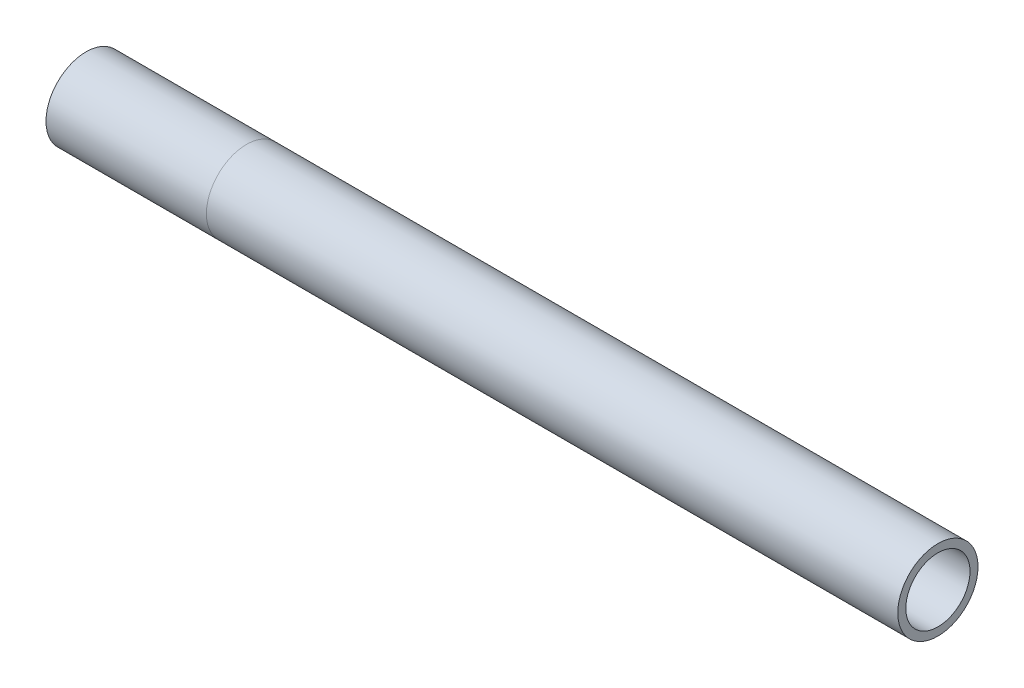
SolidWorks part; units mm, degrees
ref_plane "Front Plane" through (0, 0, 0) normal (0, 0, 1) x (1, 0, 0)
ref_plane "Top Plane" through (0, 0, 0) normal (0, 1, 0) x (1, 0, 0)
ref_plane "Right Plane" through (0, 0, 0) normal (1, 0, 0) x (0, 0, -1)
sketch "Sketch2" plane through (0, 0, 0) normal (0, 0, 1) x (1, 0, 0)
  line L0 (-77.8723, 14.641) -> (125.953, 14.641) construction
  line L1 (-107.3181, 25.8935) -> (-56.5181, 25.8935)
  line L2 (-56.5181, 25.8935) -> (162.4299, 25.8935)
  line L3 (162.4299, 25.8935) -> (162.4299, -141.1032) construction
  line L4 (-56.5181, 25.8935) -> (-56.5181, -136.7296) construction
  line L5 (189.8569, 74.1051) -> (189.8569, -336.1283) construction
  dimension "D1" = 180
  dimension "D2" = 50.8
  dimension "D3" = 218.948
ref_plane "Plane1" through (-107.3181, 25.8935, 0) normal (1, 0, 0) x (0, 1, 0)
ref_plane "Plane2" through (-56.5181, 25.8935, 0) normal (1, 0, 0) x (0, 1, 0)
other "Tubing TUBING(1)"
ref_plane "Plane3" through (-107.3181, 25.8935, 0) normal (1, 0, 0) x (0, 1, 0)
sketch "Sketch1" plane through (-107.3181, 25.8935, 0) normal (1, 0, 0) x (0, 1, 0)
  circle A0 centre (0, 0) radius 12.7
  circle A1 centre (0, 0) radius 10.16
  point P5 (0, 12.7)
  point P6 (0, 10.16)
  point P7 (0, -12.7)
  point P8 (0, -10.16)
  point P9 (0, 0)
  dimension "D1" = 25.4
  dimension "D2" = 2.54
sketch "Sketch5" plane through (-107.3181, 25.8935, 0) normal (1, 0, 0) x (0, 1, 0)
  line L0 (12.7, 0) -> (-12.7, 0) construction
  circle A0 centre (0, 0) radius 12.7 construction
  circle A1 centre (0, 0) radius 10.16 construction
  point P5 (-10.16, 0)
sketch "Sketch6" plane through (162.4299, 0, 0) normal (1, 0, 0) x (0, 0, -1)
  line L0 (0, 38.5935) -> (0, 13.1935) construction
  circle A0 centre (0, 25.8935) radius 12.7 construction
